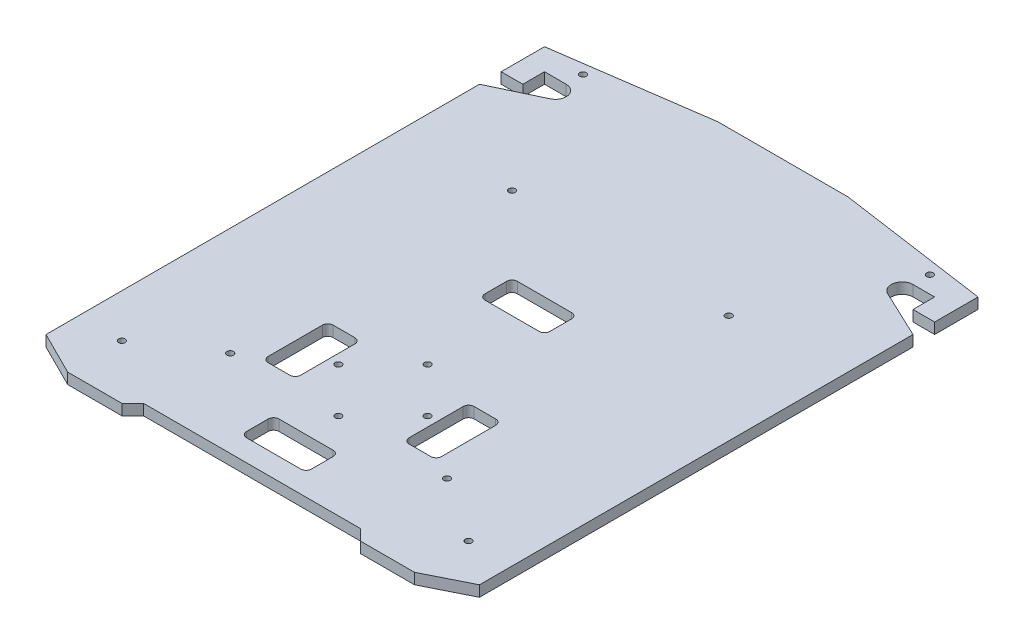
SolidWorks part; units mm, degrees
ref_plane "前视基准面" through (0, 0, 0) normal (0, 0, 1) x (1, 0, 0)
ref_plane "上视基准面" through (0, 0, 0) normal (0, 1, 0) x (1, 0, 0)
ref_plane "右视基准面" through (0, 0, 0) normal (1, 0, 0) x (0, 0, -1)
sketch "草图1" plane through (0, 0, 0) normal (0, 1, 0) x (1, 0, 0)
  line L0 (-101.2883, 0) -> (102.7951, 0) construction
  line L1 (0, 100.6692) -> (0, -107.1144) construction
  line L3 (-100, 125) -> (100, 125)
  line L4 (-100, 125) -> (-100, -125)
  line L5 (-100, -125) -> (100, -125)
  line L6 (100, 125) -> (100, -125)
  dimension "D1" = 250
  dimension "D2" = 200
extrude "凸台-拉伸1" add sketch "草图1" along normal blind 5
sketch "草图2" plane through (0, 5, 0) normal (0, 1, 0) x (1, 0, 0)
  line L0 (-100, -115) -> (-80, -125)
  line L1 (-100, 125) -> (-100, -125) construction
  line L2 (-100, -125) -> (100, -125) construction
  line L3 (-80, -125) -> (-100, -125)
  line L4 (-100, -125) -> (-100, -115)
  dimension "D1" = 10
  dimension "D2" = 20
extrude "切除-拉伸1" cut sketch "草图2" against normal blind 35
mirror "镜向1" about plane through (0, 0, 0) normal (1, 0, 0) of "切除-拉伸1"
sketch "草图3" plane through (0, 5, 0) normal (0, 1, 0) x (1, 0, 0)
  line L1 (-80, -125) -> (80, -125) construction
  line L2 (-55, -125) -> (-50, -120)
  line L3 (-50, -120) -> (0, -120)
  line L4 (0, -2.75) -> (0, 2.75) construction
  line L5 (0, -120) -> (0, -125)
  line L6 (0, -125) -> (-55, -125)
  dimension "D2" = 5
  dimension "D3" = 45
extrude "切除-拉伸2" cut sketch "草图3" against normal blind 35
mirror "镜向2" about plane through (0, 0, 0) normal (1, 0, 0) of "切除-拉伸2"
sketch "草图4" plane through (0, 5, 0) normal (0, 1, 0) x (1, 0, 0)
  line L1 (-12.5, -95) -> (12.5, -95)
  line L2 (-15, -97.5) -> (-15, -107.5)
  line L3 (-12.5, -110) -> (12.5, -110)
  line L4 (15, -97.5) -> (15, -107.5)
  line L5 (50, -120) -> (-50, -120) construction
  line L6 (0, -2.75) -> (0, 2.75) construction
  arc A0 (12.5, -110) -> (15, -107.5) centre (12.5, -107.5) ccw
  arc A1 (15, -97.5) -> (12.5, -95) centre (12.5, -97.5) ccw
  arc A2 (-12.5, -95) -> (-15, -97.5) centre (-12.5, -97.5) ccw
  arc A3 (-12.5, -110) -> (-15, -107.5) centre (-12.5, -107.5) cw
  point P10 (15, -110)
  point P13 (15, -95)
  dimension "D5" = 2.5
  dimension "D1" = 10
  dimension "D2" = 15
  dimension "D3" = 15
  dimension "D4" = 15
extrude "切除-拉伸3" cut sketch "草图4" against normal blind 35
sketch "草图5" plane through (0, 0, 0) normal (0, 1, 0) x (1, 0, 0)
  line L0 (-30, 125) -> (-100, 115)
  line L1 (100, 125) -> (-100, 125) construction
  line L2 (-100, 125) -> (-100, -115) construction
  line L3 (-100, 115) -> (-100, 125)
  line L4 (-100, 125) -> (-30, 125)
  line L5 (0, -2.75) -> (0, 2.75) construction
  dimension "D1" = 30
  dimension "D2" = 10
extrude "切除-拉伸5" cut sketch "草图5" along normal blind 30
mirror "镜向3" about plane through (0, 0, 0) normal (1, 0, 0) of "切除-拉伸5"
sketch "草图6" plane through (0, 5, 0) normal (0, 1, 0) x (1, 0, 0)
  line L0 (-100, 95) -> (-90, 95)
  line L1 (-100, 115) -> (-100, -115) construction
  line L2 (-90, 95) -> (-90, 105)
  line L3 (-90, 105) -> (-80, 105)
  line L4 (-100, 95) -> (-100, 85)
  line L5 (-100, 85) -> (-77.8606, 95.4808)
  arc A0 (-77.8606, 95.4808) -> (-80, 105) centre (-80, 100) ccw
  dimension "D5" = 10
  dimension "D1" = 20
  dimension "D2" = 10
  dimension "D3" = 10
  dimension "D4" = 10
  dimension "D6" = 10
extrude "切除-拉伸6" cut sketch "草图6" against normal blind 10
mirror "镜向4" about plane through (0, 0, 0) normal (1, 0, 0) of "切除-拉伸6"
sketch "草图8" plane through (0, 5, 0) normal (0, 1, 0) x (1, 0, 0)
  line L0 (12.5, -95) -> (-12.5, -95) construction
  line L1 (-37.5, -45) -> (-27.5, -45)
  line L2 (-40, -47.5) -> (-40, -72.5)
  line L3 (-37.5, -75) -> (-27.5, -75)
  line L4 (-25, -47.5) -> (-25, -72.5)
  line L5 (-100, 85) -> (-100, -115) construction
  line L6 (0, -2.75) -> (0, 2.75) construction
  line L7 (25, -47.5) -> (25, -72.5)
  line L8 (37.5, -75) -> (27.5, -75)
  line L9 (40, -47.5) -> (40, -72.5)
  line L10 (37.5, -45) -> (27.5, -45)
  line L11 (-2.75, 0) -> (2.75, 0) construction
  line L12 (-12.5, 15) -> (12.5, 15)
  line L13 (-15, 12.5) -> (-15, 2.5)
  line L14 (-12.5, 0) -> (12.5, 0)
  line L15 (15, 12.5) -> (15, 2.5)
  arc A0 (-40, -72.5) -> (-37.5, -75) centre (-37.5, -72.5) ccw
  arc A1 (-27.5, -75) -> (-25, -72.5) centre (-27.5, -72.5) ccw
  arc A2 (-25, -47.5) -> (-27.5, -45) centre (-27.5, -47.5) ccw
  arc A3 (-40, -47.5) -> (-37.5, -45) centre (-37.5, -47.5) cw
  arc A4 (40, -47.5) -> (37.5, -45) centre (37.5, -47.5) ccw
  arc A5 (25, -47.5) -> (27.5, -45) centre (27.5, -47.5) cw
  arc A6 (27.5, -75) -> (25, -72.5) centre (27.5, -72.5) cw
  arc A7 (40, -72.5) -> (37.5, -75) centre (37.5, -72.5) cw
  arc A8 (12.5, 15) -> (15, 12.5) centre (12.5, 12.5) cw
  arc A9 (15, 2.5) -> (12.5, 0) centre (12.5, 2.5) cw
  arc A10 (-12.5, 0) -> (-15, 2.5) centre (-12.5, 2.5) cw
  arc A11 (-15, 12.5) -> (-12.5, 15) centre (-12.5, 12.5) cw
  point P6 (-40, -75)
  point P9 (-25, -75)
  point P14 (-40, -45)
  point P33 (40, -45)
  point P34 (25, -75)
  point P35 (40, -75)
  point P46 (15, 0)
  point P49 (-15, 0)
  point P52 (-15, 15)
  dimension "D3" = 2.5
  dimension "D9" = 2.5
  dimension "D1" = 30
  dimension "D2" = 15
  dimension "D4" = 20
  dimension "D5" = 60
  dimension "D6" = 15
  dimension "D7" = 15
  dimension "D8" = 15
extrude "切除-拉伸7" cut sketch "草图8" against normal blind 10
sketch "草图9" plane through (0, 5, 0) normal (0, 1, 0) x (1, 0, 0)
  line L0 (-100, 85) -> (-100, -115) construction
  line L2 (-80, -125) -> (-55, -125) construction
  line L3 (0, -2.75) -> (0, 2.75) construction
  circle A0 centre (-80, -100) radius 1.5
  circle A1 centre (80, -100) radius 1.5
  dimension "D3" = 3
  dimension "D1" = 20
  dimension "D2" = 25
extrude "切除-拉伸8" cut sketch "草图9" against normal blind 10
sketch "草图10" plane through (0, 5, 0) normal (0, 1, 0) x (1, 0, 0)
  line L0 (-100, 115) -> (-100, 95) construction
  line L1 (-30, 125) -> (-100, 115) construction
  line L2 (0, -2.75) -> (0, 2.75) construction
  circle A0 centre (-80, 112.8064) radius 1.5
  circle A1 centre (80, 112.8064) radius 1.5
  dimension "D3" = 3
  dimension "D1" = 20
  dimension "D2" = 5
extrude "切除-拉伸9" cut sketch "草图10" against normal blind 10
sketch "草图12" plane through (0, 5, 0) normal (0, 1, 0) x (1, 0, 0)
  circle A1 centre (0, -38.9121) radius 1.5
  circle A2 centre (-20.6062, -59.5182) radius 1.5
  circle A3 centre (20.6062, -59.5182) radius 1.5
  circle A4 centre (0, -80.1244) radius 1.5
  dimension "D1" = 3
  dimension "D2" = 3
  dimension "D3" = 3
  dimension "D4" = 3
extrude "切除-拉伸10" cut sketch "草图12" against normal blind 10
sketch "草图13" plane through (0, 5, 0) normal (0, 1, 0) x (1, 0, 0)
  line L0 (-100, 85) -> (-100, -115) construction
  line L1 (-80, -125) -> (-55, -125) construction
  line L2 (0, -2.75) -> (0, 2.75) construction
  circle A0 centre (-50, -80) radius 1.5
  circle A1 centre (50, -80) radius 1.5
  circle A2 centre (-50, 50) radius 1.5
  circle A3 centre (50, 50) radius 1.5
  dimension "D1" = 3
  dimension "D4" = 3
  dimension "D2" = 50
  dimension "D3" = 45
  dimension "D5" = 130
extrude "切除-拉伸11" cut sketch "草图13" against normal blind 10
ref_plane "基准面1" through (0, 0, 60) normal (0, 0, 1) x (1, 0, 0)
